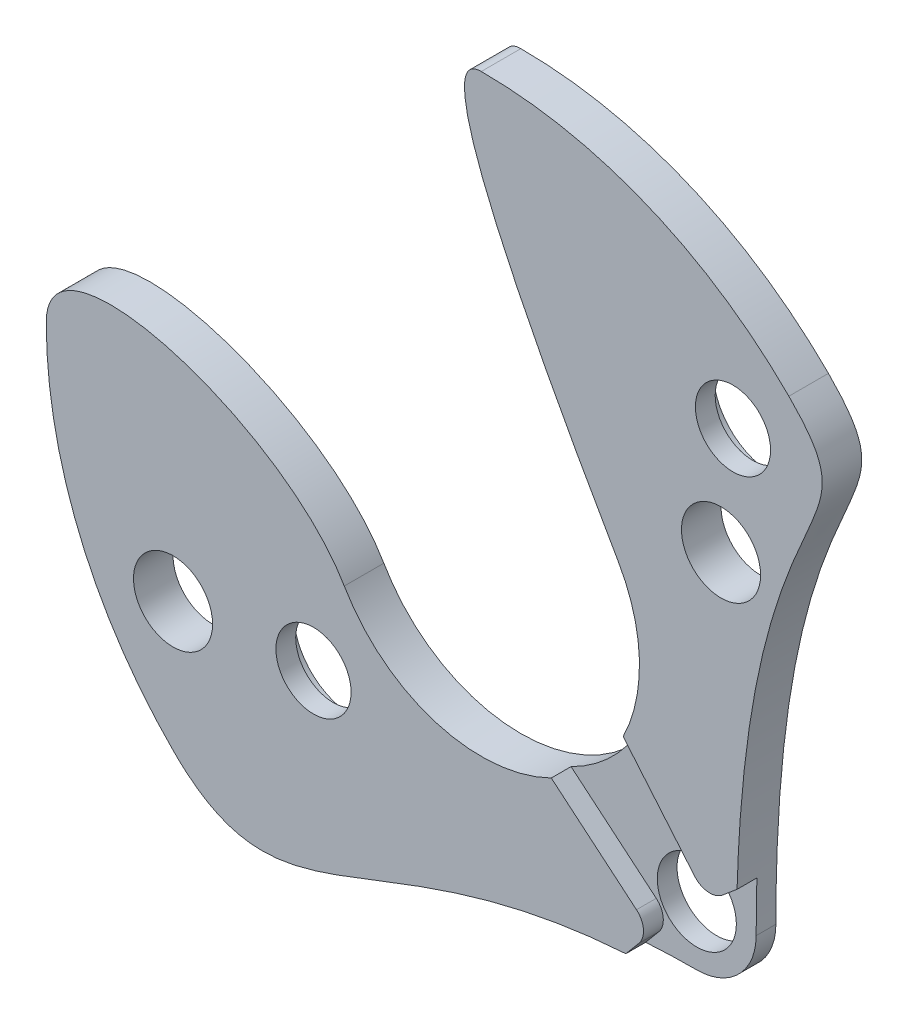
SolidWorks part; units mm, degrees
ref_plane "Alzado" through (0, 0, 0) normal (0, 0, 1) x (1, 0, 0)
ref_plane "Planta" through (0, 0, 0) normal (0, 1, 0) x (1, 0, 0)
ref_plane "Vista lateral" through (0, 0, 0) normal (1, 0, 0) x (0, 0, -1)
sketch "Croquis1" plane through (0, 0, 0) normal (0, 0, 1) x (1, 0, 0)
  line L0 (-4.3301, -2.5) -> (3.4641, 2) construction
  line L1 (0, 0) -> (2.4749, -2.4749) construction
  line L2 (0, 0) -> (5.5, 0) construction
  arc A0 (4.1761, 3.5791) -> (0, 5.5) centre (0, 0) ccw
  arc A1 (-1.7321, -1) -> (1.7321, 1) centre (0, 0) ccw
  circle A2 centre (2.4749, -2.4749) radius 0.5
  circle A3 centre (3.0311, 1.75) radius 0.5
  circle A4 centre (-3.8971, -2.25) radius 0.5
  arc A5 (-5.5, 0) -> (-3.8891, -3.8891) centre (0, 0) ccw
  arc A7 (2.4749, -3.2249) -> (3.2249, -2.4749) centre (2.4749, -2.4749) ccw
  spline S0 degree 3 poles (3.8891, 3.8891) (5.1329, 2.6453) (3.2249, 3.0146) (3.2249, -2.4749) knots 0 0 0 0 0.763897 0.763897 0.763897 0.763897
  spline S1 degree 3 poles (2.4749, -3.2249) (-1.3587, -3.2249) (-2.389, -5.3892) (-3.8891, -3.8891) knots 0 0 0 0 1 1 1 1
  spline S2 degree 3 poles (1.7321, 1) (0.9487, 2.3568) (-0.8208, 5.5) (0, 5.5) knots 0 0 0 0 1 1 1 1
  spline S3 degree 3 poles (-1.7321, -1) (-2.5154, 0.3568) (-5.5, 1.2621) (-5.5, 0) knots 0 0 0 0 1 1 1 1
  dimension "D1" = 11
  dimension "D2" = 4
  dimension "D4" = 3.5
  dimension "D5" = 1
  dimension "D6" = 45
  dimension "D8" = 1
  dimension "D11" = 1.5
  dimension "D7" = 1
  dimension "D3" = 30
  dimension "D10" = 4.5
  dimension "D12" = 3.5
extrude "Saliente-Extruir1" add sketch "Croquis1" along normal blind 0.5
sketch "Croquis3" plane through (0, 0, 0) normal (0, 0, -1) x (-1, 0, 0)
  line L0 (-3.182, 3.182) -> (2.1213, -2.1213) construction
  line L2 (-2.4749, -2.4749) -> (0, 0) construction
  circle A0 centre (-3.182, 3.182) radius 0.75
  circle A1 centre (2.1213, -2.1213) radius 0.75
  dimension "D1" = 1.5
  dimension "D2" = 1.5
  dimension "D3" = 90
  dimension "D4" = 3
  dimension "D5" = 4.5
extrude "Cortar-Extruir1" cut sketch "Croquis3" against normal blind 0.25
sketch "Croquis4" plane through (0, 0, 0.5) normal (0, 0, 1) x (1, 0, 0)
  line L0 (0, 0) -> (2.4749, -2.4749) construction
  line L1 (2.4749, -2.4749) -> (0.04, 0.4269) construction
  line L2 (2.4749, -2.4749) -> (-0.3404, -0.1126) construction
  line L3 (2.6972, -1.962) -> (1.7935, -0.885)
  line L4 (1.962, -2.6972) -> (0.885, -1.7935)
  line L5 (3.0494, -1.9928) -> (3.2339, -1.838)
  line L6 (2.8579, -2.1535) -> (0.423, 0.7483) construction
  line L7 (2.1535, -2.8579) -> (-0.6618, -0.4956) construction
  line L8 (1.9928, -3.0494) -> (1.8277, -3.2461)
  circle A0 centre (2.4749, -2.4749) radius 0.5 construction
  arc A1 (-1.7321, -1) -> (1.7321, 1) centre (0, 0) ccw construction
  arc A2 (0.885, -1.7935) -> (1.7935, -0.885) centre (0, 0) ccw
  arc A3 (2.4749, -3.2249) -> (3.2249, -2.4749) centre (2.4749, -2.4749) ccw construction
  arc A4 (2.4749, -3.2249) -> (3.2249, -2.4749) centre (2.4749, -2.4749) ccw
  arc A5 (1.9928, -3.0494) -> (1.962, -2.6972) centre (1.8013, -2.8887) ccw
  arc A6 (3.0494, -1.9928) -> (2.6972, -1.962) centre (2.8887, -1.8013) cw
  spline S0 degree 3 poles (-1254.9331, 1557.4287) (1168.5362, -1596.7176) (-1057.245, 1672.0674) (955.1385, -1760.4826) knots -4.345729 -4.345729 -4.345729 -4.345729 4.871085 4.871085 4.871085 4.871085 only from (3.8891, 3.8891) to (3.2249, -2.4749) construction
  spline S1 degree 3 poles (1167.5656, -1627.4232) (-1014.5672, 1701.0285) (905.2633, -1771.8581) (-851.953, 1807.0931) knots -6.180586 -6.180586 -6.180586 -6.180586 7.164534 7.164534 7.164534 7.164534 only from (2.4749, -3.2249) to (-3.8891, -3.8891) construction
  spline S2 degree 3 poles (3.2339, -1.838) (3.228, -2.0411) (3.2249, -2.2532) (3.2249, -2.4749) knots 0.733048 0.733048 0.733048 0.733048 0.763897 0.763897 0.763897 0.763897
  spline S3 degree 3 poles (2.4749, -3.2249) (2.2497, -3.2249) (2.0342, -3.2323) (1.8277, -3.2461) knots 0 0 0 0 0.058734 0.058734 0.058734 0.058734
  dimension "D5" = 0.25
  dimension "D1" = 5
  dimension "D2" = 5
  dimension "D3" = 0.5
  dimension "D4" = 0.5
extrude "Cortar-Extruir2" cut sketch "Croquis4" against normal blind 0.25
hole_wizard "Taladro roscado M1.2x0.251" positions "Croquis6" profile "Croquis5" tap size "M1.2x0.25" standard "ISO" end condition through all
sketch "Croquis6" plane through (0, 0, 0.25) normal (0, 0, -1) x (-1, 0, 0)
  circle A0 centre (2.1213, -2.1213) radius 0.75 construction
  point P0 (2.1213, -2.1213)
  point P1 (-3.182, 3.182)
sketch "Croquis5" plane through (-2.1213, -2.1213, 0.25) normal (1, 0, 0) x (0, 1, 0)
  line L0 (0, 0) -> (0, 0.25)
  line L1 (0, 0.25) -> (0.475, 0.25)
  line L2 (0.475, 0.25) -> (0.475, 0)
  line L5 (0.475, 0) -> (0, 0)
  line L11 (0, -6.35) -> (0, 107.95) construction
  dimension "Diámetro de perforador para roscar hasta el siguiente" = 0.95
  dimension "Profundidad de perforador para roscar hasta el siguiente" = 0.2501
cosmetic thread "Rosca de taladro1" parameters "D2"=1.2
cosmetic thread "Rosca de taladro2" parameters "D2"=1.2
